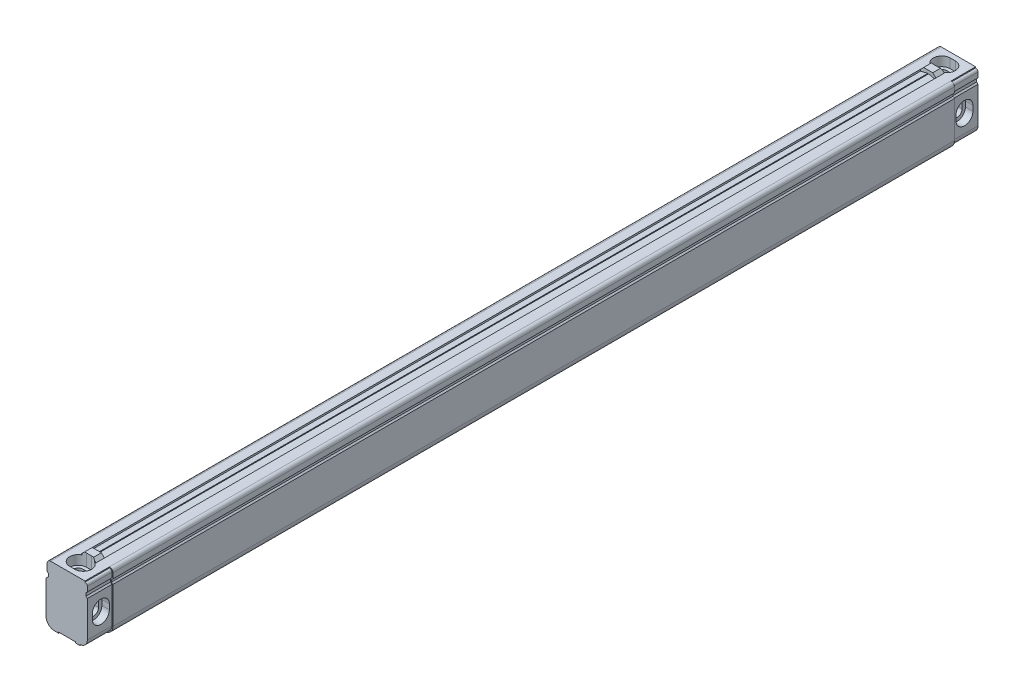
SolidWorks part; units mm, degrees
material "1060 Сплав"
ref_plane "Спереди" through (0, 0, 0) normal (0, 0, 1) x (1, 0, 0)
ref_plane "Сверху" through (0, 0, 0) normal (0, 1, 0) x (1, 0, 0)
ref_plane "Справа" through (0, 0, 0) normal (1, 0, 0) x (0, 0, -1)
sketch "Эскиз1" plane through (0, 0, 0) normal (0, 0, 1) x (1, 0, 0)
  line L0 (-11.8, 32.5) -> (-11.8, 28.3)
  line L1 (-11, 26) -> (-12.5, 24.5)
  line L2 (12.5, 5) -> (12.5, 26.5)
  line L3 (10.5, 34.5) -> (-9.8, 34.5)
  line L4 (-12.5, 24.5) -> (-12.5, 5)
  line L5 (-7.5, 0) -> (7.5, 0)
  line L6 (0, 0) -> (0, -9.9877) construction
  line L8 (12.5, 32.5) -> (12.5, 29.3)
  line L9 (11.7, 28.5) -> (11.7, 27.3)
  line L11 (12.5, 26.5) -> (11.7, 27.3)
  line L12 (12.5, 29.3) -> (11.7, 28.5)
  line L13 (-11.8, 28.3) -> (-11, 27.5)
  line L14 (-11, 27.5) -> (-11, 26)
  arc A1 (7.5, 0) -> (12.5, 5) centre (7.5, 5) ccw
  arc A2 (-12.5, 5) -> (-7.5, 0) centre (-7.5, 5) ccw
  arc A3 (10.5, 34.5) -> (12.5, 32.5) centre (10.5, 32.5) cw
  arc A4 (-11.8, 32.5) -> (-9.8, 34.5) centre (-9.8, 32.5) cw
  dimension "D4" = 0.8
  dimension "D6" = 5
  dimension "D12" = 2
  dimension "D1" = 45
  dimension "D2" = 24.3
  dimension "D3" = 10
  dimension "D5" = 8
  dimension "D7" = 25
  dimension "D8" = 34.5
  dimension "D9" = 7
  dimension "D10" = 6
  dimension "D11" = 1.5
extrude "Бобышка-Вытянуть1" add sketch "Эскиз1" along normal blind 526
sketch "Эскиз2" plane through (0, 0, 0) normal (0, 0, -1) x (-1, 0, 0)
  line L5 (-10.5, 33.9) -> (-10.5, 34.5)
  line L6 (-12.5, 5) -> (-12.5, 26.5) construction
  line L7 (-12.5, 26.5) -> (-11.7, 27.3) construction
  line L8 (-11.7, 27.3) -> (-11.7, 28.5) construction
  line L9 (-11.7, 28.5) -> (-12.5, 29.3) construction
  line L10 (-11.9, 26.2515) -> (-11.9, 5)
  line L11 (-11.1, 27.0515) -> (-11.9, 26.2515)
  line L12 (-11.1, 28.7485) -> (-11.1, 27.0515)
  line L13 (-11.9, 29.5485) -> (-11.1, 28.7485)
  line L14 (-11.9, 32.5) -> (-11.9, 29.5485)
  line L15 (-11.9, 26.2515) -> (-11.9, 5)
  line L16 (-11.1, 27.0515) -> (-11.9, 26.2515)
  line L17 (-11.1, 28.7485) -> (-11.1, 27.0515)
  line L18 (-11.9, 29.5485) -> (-11.1, 28.7485)
  line L19 (-11.9, 32.5) -> (-11.9, 29.5485)
  line L20 (-12.5, 29.3) -> (-12.5, 32.5) construction
  line L21 (-12.5, 5) -> (-12.5, 26.5)
  line L22 (-12.5, 26.5) -> (-11.7, 27.3)
  line L23 (-11.7, 27.3) -> (-11.7, 28.5)
  line L24 (-11.7, 28.5) -> (-12.5, 29.3)
  line L25 (-12.5, 29.3) -> (-12.5, 32.5)
  line L26 (-7.5, 0.6) -> (-7.5, 0)
  line L27 (7.5, 0) -> (-7.5, 0) construction
  line L28 (-5, 0) -> (5, 0)
  line L29 (-5, 0) -> (-5, 0.6)
  line L30 (-5, 0.6) -> (5, 0.6)
  line L31 (5, 0) -> (5, 0.6)
  line L32 (12.5, 24.5) -> (12.5, 5) construction
  arc A2 (-10.5, 34.5) -> (-12.5, 32.5) centre (-10.5, 32.5) ccw construction
  arc A3 (-10.5, 34.5) -> (-12.5, 32.5) centre (-10.5, 32.5) ccw
  arc A4 (-11.9, 5) -> (-7.5, 0.6) centre (-7.5, 5) ccw
  arc A5 (-10.5, 33.9) -> (-11.9, 32.5) centre (-10.5, 32.5) ccw
  arc A6 (-11.9, 5) -> (-7.5, 0.6) centre (-7.5, 5) ccw
  arc A7 (-10.5, 33.9) -> (-11.9, 32.5) centre (-10.5, 32.5) ccw
  arc M12 (-12.5, 5) -> (-7.5, 0) centre (-7.5, 5) ccw
  line M13 (-7.5, 0) -> (7.5, 0)
  arc M22 (-10.5, 34.5) -> (-12.5, 32.5) centre (-10.5, 32.5) ccw
  line M23 (-12.5, 32.5) -> (-12.5, 29.3)
  line M24 (-12.5, 29.3) -> (-11.7, 28.5)
  line M25 (-11.7, 28.5) -> (-11.7, 27.3)
  line M26 (-11.7, 27.3) -> (-12.5, 26.5)
  line M27 (-12.5, 26.5) -> (-12.5, 5)
  dimension "D2" = 7.5
  dimension "D3" = 7.5
  dimension "D1" = 0.6
extrude "Вырез-Вытянуть1" cut sketch "Эскиз2" against normal blind 14.5 contours A7 L5 L26 A6 L15 L16 L17 L18 L19 M22 M23 M24 M25 M26 M27 M12 | L31 L30 L29 M13
sketch "Эскиз5" plane through (0, 0, 526) normal (0, 0, 1) x (1, 0, 0)
  line L0 (0, 34.5) -> (0, 37.905) construction
  line L1 (10.5, 34.5) -> (-9.8, 34.5) construction
  line L2 (-4.5, 34.5) -> (-2.7, 36.3)
  line L3 (-2.7, 36.3) -> (2.7, 36.3)
  line L4 (4.5, 34.5) -> (2.7, 36.3)
  line L5 (4.5, 34.5) -> (-4.5, 34.5)
  line L7 (-7.5, 0) -> (7.5, 0) construction
  line L9 (-12.5, 24.5) -> (-12.5, 5) construction
  line L10 (12.5, 29.3) -> (12.5, 32.5) construction
  dimension "D1" = 36.3
  dimension "D2" = 8
  dimension "D3" = 8
  dimension "D4" = 45
extrude "Бобышка-Вытянуть2" add sketch "Эскиз5" against normal blind 5 from offset 12.5 offset against normal yes
ref_plane "Плоскость1" through (0, 0, 263) normal (0, 0, 1) x (1, 0, 0)
mirror "Зеркальное отражение1" about plane through (0, 0, 263) normal (0, 0, 1) of "Бобышка-Вытянуть2", "Вырез-Вытянуть1"
sketch "Эскиз3" plane through (11.9, 0, 0) normal (1, 0, 0) x (0, 0, -1)
  line L0 (-518, 14) -> (-518, 17) construction
  line L1 (-523, 14) -> (-523, 17)
  line L2 (-513, 14) -> (-513, 17)
  line L3 (-263, 26.5) -> (-263, 5) construction
  line L4 (-511.5, 26.5) -> (-14.5, 26.5) construction
  line L5 (-511.5, 5) -> (-14.5, 5) construction
  line L6 (-8, 14) -> (-8, 17) construction
  line L7 (-3, 14) -> (-3, 17)
  line L8 (-13, 14) -> (-13, 17)
  line L9 (-14.5, 0) -> (0, 0) construction
  line L10 (-14.5, 34.5) -> (0, 34.5) construction
  line L11 (-518, 22) -> (-518, 34.5) construction
  line L12 (-526, 34.5) -> (-511.5, 34.5) construction
  line L13 (-518, 9) -> (-518, 0) construction
  line L14 (-526, 0) -> (-511.5, 0) construction
  arc A0 (-523, 14) -> (-513, 14) centre (-518, 14) ccw
  arc A1 (-513, 17) -> (-523, 17) centre (-518, 17) ccw
  arc A2 (-3, 14) -> (-13, 14) centre (-8, 14) cw
  arc A3 (-13, 17) -> (-3, 17) centre (-8, 17) cw
  point P2 (-518, 15.5)
  point P15 (-8, 15.5)
  dimension "D1" = 5
  dimension "D6" = 14
  dimension "D2" = 510
  dimension "D3" = 3
  dimension "D4" = 9
  dimension "D5" = 17.5
  dimension "D7" = 9
  dimension "D8" = 12.5
  dimension "D9" = 34.5
extrude "Вырез-Вытянуть2" cut sketch "Эскиз3" against normal blind 4.4
sketch "Эскиз4" plane through (12.5, 0, 0) normal (1, 0, 0) x (0, 0, -1)
  line L0 (-518, 14) -> (-518, 17) construction
  line L1 (-521, 14) -> (-521, 17)
  line L2 (-515, 14) -> (-515, 17)
  line L3 (-518, 20) -> (-518, 34.5) construction
  line L4 (-526, 34.5) -> (-511.5, 34.5) construction
  line L5 (-518, 11) -> (-518, 20) construction
  line L6 (-518, 11) -> (-518, 0) construction
  line L7 (-526, 0) -> (-511.5, 0) construction
  line L8 (-263, 5) -> (-263, 26.5) construction
  line L9 (-511.5, 5) -> (-14.5, 5) construction
  line L10 (-511.5, 26.5) -> (-14.5, 26.5) construction
  line L11 (-8, 14) -> (-8, 17) construction
  line L12 (-5, 14) -> (-5, 17)
  line L13 (-11, 14) -> (-11, 17)
  arc A0 (-521, 14) -> (-515, 14) centre (-518, 14) ccw
  arc A1 (-515, 17) -> (-521, 17) centre (-518, 17) ccw
  arc A2 (-523, 14) -> (-513, 14) centre (-518, 14) ccw construction
  arc A3 (-513, 17) -> (-523, 17) centre (-518, 17) ccw construction
  arc A4 (-5, 14) -> (-11, 14) centre (-8, 14) cw
  arc A5 (-11, 17) -> (-5, 17) centre (-8, 17) cw
  point P2 (-518, 15.5)
  point P29 (-8, 15.5)
  dimension "D1" = 3
  dimension "D2" = 14.5
  dimension "D3" = 3
  dimension "D4" = 9
  dimension "D5" = 11
extrude "Вырез-Вытянуть3" cut sketch "Эскиз4" against normal through all
sketch "Эскиз6" plane through (0, 34.5, 0) normal (0, 1, 0) x (1, 0, 0)
  line L0 (-1.5, -8) -> (1.5, -8) construction
  line L1 (-1.5, -3) -> (1.5, -3)
  line L2 (-1.5, -13) -> (1.5, -13)
  line L3 (0, -17.5) -> (0, -8) construction
  line L4 (-4.5, -17.5) -> (4.5, -17.5) construction
  line L5 (10.5, 0) -> (-9.8, 0) construction
  line L6 (-1.5, -518) -> (1.5, -518) construction
  line L7 (-1.5, -513) -> (1.5, -513)
  line L8 (-1.5, -523) -> (1.5, -523)
  line L9 (10.5, -526) -> (-9.8, -526) construction
  arc A0 (-1.5, -3) -> (-1.5, -13) centre (-1.5, -8) ccw
  arc A1 (1.5, -13) -> (1.5, -3) centre (1.5, -8) ccw
  arc A2 (-1.5, -513) -> (-1.5, -523) centre (-1.5, -518) ccw
  arc A3 (1.5, -523) -> (1.5, -513) centre (1.5, -518) ccw
  point P2 (0, -8)
  point P11 (0, -518)
  dimension "D1" = 5
  dimension "D2" = 3
  dimension "D3" = 3
  dimension "D4" = 3
extrude "Вырез-Вытянуть4" cut sketch "Эскиз6" against normal blind 5.5 and the other way blind 5.5
sketch "Эскиз7" plane through (0, 34.5, 0) normal (0, 1, 0) x (1, 0, 0)
  line L0 (-1.5, -518) -> (1.5, -518) construction
  line L1 (-1.5, -515) -> (1.5, -515)
  line L2 (-1.5, -521) -> (1.5, -521)
  line L3 (-1.5, -8) -> (1.5, -8) construction
  line L4 (-1.5, -5) -> (1.5, -5)
  line L5 (-1.5, -11) -> (1.5, -11)
  arc A0 (-1.5, -515) -> (-1.5, -521) centre (-1.5, -518) ccw
  arc A1 (1.5, -521) -> (1.5, -515) centre (1.5, -518) ccw
  arc A2 (1.5, -523) -> (1.5, -513) centre (1.5, -518) ccw construction
  arc A3 (-3.6794, -513.5) -> (-1.5, -523) centre (-1.5, -518) ccw construction
  arc A4 (-1.5, -5) -> (-1.5, -11) centre (-1.5, -8) ccw
  arc A5 (1.5, -11) -> (1.5, -5) centre (1.5, -8) ccw
  arc A6 (3.6794, -12.5) -> (1.5, -3) centre (1.5, -8) ccw construction
  arc A7 (-1.5, -3) -> (-1.5, -13) centre (-1.5, -8) ccw construction
  point P2 (0, -518)
  point P15 (0, -8)
  dimension "D1" = 3
extrude "Вырез-Вытянуть5" cut sketch "Эскиз7" against normal through all
sketch "Эскиз8" plane through (0, 0, 17.5) normal (0, 0, 1) x (1, 0, 0)
  line L0 (-4.5, 34.5) -> (-4.5, 33.5)
  line L1 (-4.5, 33.5) -> (-0.25, 34.5)
  line L2 (-4.5, 34.5) -> (4.5, 34.5) construction
  line L3 (-0.25, 34.5) -> (-0.25, 33.5)
  line L4 (-0.25, 33.5) -> (0.25, 33.5)
  line L5 (0, 36.3) -> (0, 34.5) construction
  line L6 (2.7, 36.3) -> (-2.7, 36.3) construction
  line L7 (0.25, 34.5) -> (0.25, 33.5)
  line L8 (4.5, 33.5) -> (0.25, 34.5)
  line L9 (4.5, 34.5) -> (4.5, 33.5)
  line L10 (-4.5, 34.5) -> (-0.25, 34.5)
  line L11 (4.5, 34.5) -> (0.25, 34.5)
  line M9 (-4.5, 34.5) -> (4.5, 34.5)
  dimension "D1" = 0.5
  dimension "D2" = 1
extrude "Вырез-Вытянуть8" cut sketch "Эскиз8" along normal blind 491 contours L0 L1 M9 | L7 L3 L4 M9 | L9 L8 M9
equation "\"Thread_length@ThreadCosmetic\" =  (  ( sgn (  ( \"Length@BodySke\" - \"Advance@BodySke\" *  3.0  - \"Head_ht@BodySke\" )  - \"Thread_nom@BodySke\" )  - 1 )  *  (  ( \"Length@BodySke\" - \"Advance@BodySke\" *  3.0  - \"Head_ht@BodySke\" )  - \"Thread_nom@BodySke\" )  )  /  - 2 + \"Thread_nom@BodySke\""
equation "\"Num_threads\"=  int ( \"Thread_length@ThreadCosmetic\" / \"Advance@BodySke\" +  0.999  )  +  1"
